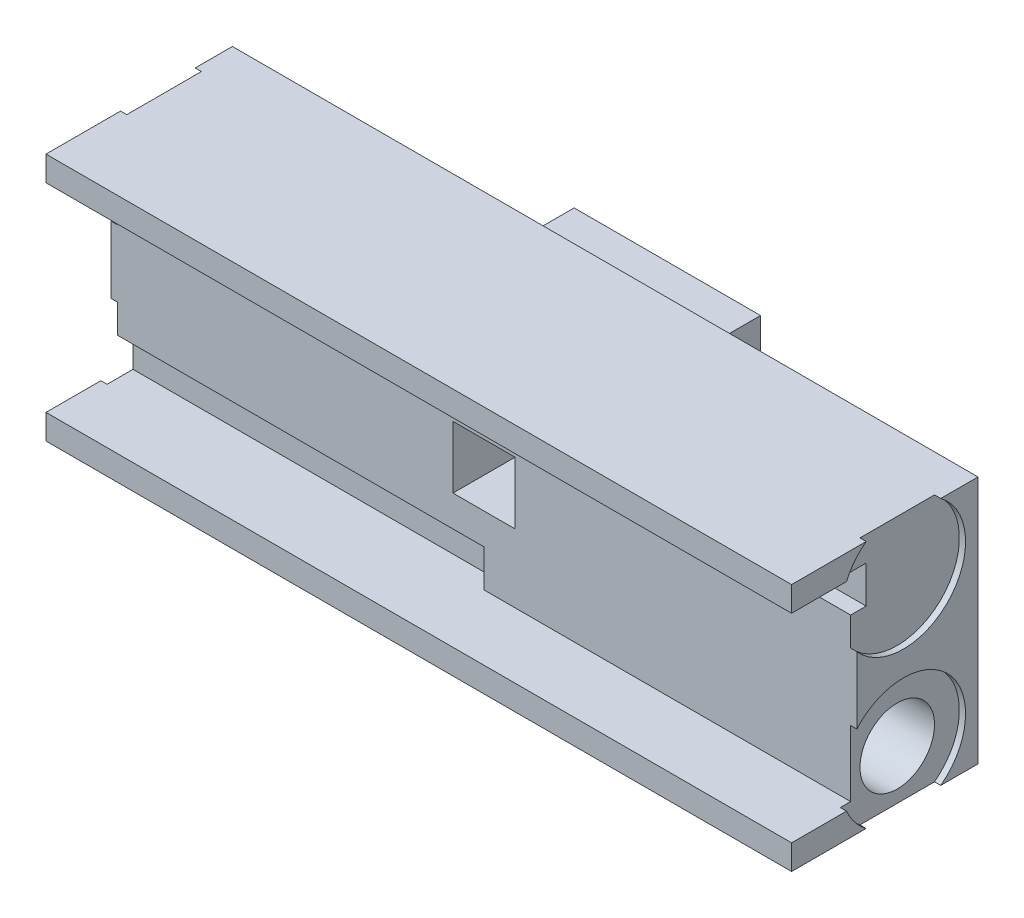
SolidWorks part; units mm, degrees
ref_plane "Front Plane" through (0, 0, 0) normal (0, 0, 1) x (1, 0, 0)
ref_plane "Top Plane" through (0, 0, 0) normal (0, 1, 0) x (1, 0, 0)
ref_plane "Right Plane" through (0, 0, 0) normal (1, 0, 0) x (0, 0, -1)
sketch "Sketch1" plane through (0, 0, 0) normal (0, 0, 1) x (1, 0, 0)
  line L1 (294.0476, 103.9123) -> (414.0476, 103.9123)
  line L2 (294.0476, 103.9123) -> (294.0476, 63.9123)
  line L3 (294.0476, 63.9123) -> (414.0476, 63.9123)
  line L4 (414.0476, 103.9123) -> (414.0476, 63.9123)
  line L5 (294.0476, 103.9123) -> (414.0476, 63.9123) construction
  line L6 (294.0476, 63.9123) -> (414.0476, 103.9123) construction
  point P0 (354.0476, 83.9123)
  dimension "D1" = 120
  dimension "D2" = 40
extrude "Boss-Extrude1" add sketch "Sketch1" along normal blind 30
sketch "Sketch2" plane through (414.0476, 0, 0) normal (1, 0, 0) x (0, 0, -1)
  line L0 (-30, 63.9123) -> (-30, 103.9123) construction
  line L1 (-30, 99.9123) -> (-19.5, 99.9123)
  line L2 (-30, 99.9123) -> (-30, 67.9123)
  line L3 (-30, 67.9123) -> (-19.5, 67.9123)
  line L4 (-19.5, 93.9123) -> (-19.5, 67.9123)
  line L5 (-30, 63.9123) -> (0, 63.9123) construction
  line L6 (-19.5, 99.9123) -> (-17, 99.9123)
  line L8 (-19.5, 93.9123) -> (-17, 93.9123)
  line L9 (-17, 99.9123) -> (-17, 93.9123)
  line L10 (-30, 103.9123) -> (0, 103.9123) construction
  dimension "D1" = 2.5
  dimension "D2" = 6
  dimension "D3" = 2.5
  dimension "D4" = 10.5
  dimension "D5" = 4
  dimension "D6" = 4
extrude "Cut-Extrude1" cut sketch "Sketch2" against normal blind 60
sketch "Sketch5" plane through (294.0476, 0, 0) normal (-1, 0, 0) x (0, 0, 1)
  line L0 (30, 103.9123) -> (30, 63.9123) construction
  line L1 (30, 99.9123) -> (19.5, 99.9123)
  line L2 (30, 99.9123) -> (30, 67.9123)
  line L3 (30, 67.9123) -> (19.5, 67.9123)
  line L4 (19.5, 99.9123) -> (19.5, 73.9123)
  line L5 (30, 63.9123) -> (0, 63.9123) construction
  line L6 (19.5, 67.9123) -> (17, 67.9123)
  line L8 (19.5, 73.9123) -> (17, 73.9123)
  line L9 (17, 67.9123) -> (17, 73.9123)
  line L10 (30, 103.9123) -> (0, 103.9123) construction
  dimension "D1" = 2.5
  dimension "D2" = 6
  dimension "D3" = 4
  dimension "D4" = 10.5
  dimension "D5" = 4
  dimension "D6" = 2.5
extrude "Cut-Extrude2" cut sketch "Sketch5" against normal blind 60
sketch "Sketch6" plane through (0, 0, 0) normal (0, 0, -1) x (-1, 0, 0)
  line L0 (-354.0476, 103.9123) -> (-354.0476, 63.9123) construction
  line L1 (-414.0476, 103.9123) -> (-294.0476, 103.9123) construction
  line L2 (-294.0476, 63.9123) -> (-414.0476, 63.9123) construction
  line L4 (-369.0476, 68.9123) -> (-339.0476, 68.9123)
  line L5 (-369.0476, 68.9123) -> (-369.0476, 98.9123)
  line L6 (-369.0476, 98.9123) -> (-339.0476, 98.9123)
  line L7 (-339.0476, 68.9123) -> (-339.0476, 98.9123)
  line L8 (-369.0476, 68.9123) -> (-339.0476, 98.9123) construction
  line L9 (-369.0476, 98.9123) -> (-339.0476, 68.9123) construction
  point P6 (-354.0476, 83.9123)
  dimension "D1" = 30
  dimension "D2" = 30
extrude "Boss-Extrude2" add sketch "Sketch6" along normal blind 10
sketch "Sketch7" plane through (414.0476, 0, 0) normal (1, 0, 0) x (0, 0, -1)
  line L0 (0, 83.9123) -> (-12, 83.9123) construction
  line L1 (0, 63.9123) -> (0, 103.9123) construction
  line L2 (-12, 83.9123) -> (-12, 95.9123) construction
  line L3 (-12, 95.9123) -> (-12, 70.5258) construction
  circle A0 centre (-12, 95.9123) radius 10
  circle A1 centre (-12, 71.9123) radius 10
  dimension "D1" = 20
  dimension "D2" = 20
  dimension "D4" = 24
  dimension "D3" = 12
  dimension "D5" = 12
extrude "Cut-Extrude3" cut sketch "Sketch7" against normal blind 1
ref_plane "Plane1" through (354.0476, 0, 0) normal (-1, 0, 0) x (0, 0, 1)
mirror "Mirror1" about plane through (354.0476, 0, 0) normal (-1, 0, 0) of "Cut-Extrude3"
sketch "Sketch9" plane through (413.0476, 0, 0) normal (1, 0, 0) x (0, 0, -1)
  line L0 (-12, 81.9123) -> (-12, 63.9123) construction
  line L1 (-18, 63.9123) -> (-6, 63.9123) construction
  line L2 (-2, 71.9123) -> (-19.5, 71.9123) construction
  line L3 (-19.5, 78.5267) -> (-19.5, 67.9123) construction
  arc A0 (-6, 63.9123) -> (-19.5, 78.5267) centre (-12, 71.9123) ccw construction
  arc A1 (-6, 63.9123) -> (-19.5, 78.5267) centre (-12, 71.9123) ccw construction
  circle A3 centre (-12, 71.9123) radius 6
  dimension "D1" = 12
  dimension "D2" = 10
  dimension "D3" = 10
  dimension "D4" = 8
extrude "Cut-Extrude4" cut sketch "Sketch9" against normal blind 35
sketch "Sketch10" plane through (295.0476, 0, 0) normal (-1, 0, 0) x (0, 0, 1)
  line L0 (18, 103.9123) -> (6, 103.9123) construction
  circle A0 centre (12, 95.9123) radius 6
  arc A1 (6, 103.9123) -> (19.5, 89.2979) centre (12, 95.9123) ccw construction
  dimension "D1" = 12
  dimension "D3" = 0
  dimension "D2" = 8
extrude "Cut-Extrude5" cut sketch "Sketch10" against normal blind 35
sketch "Sketch11" plane through (0, 0, 19.5) normal (0, 0, 1) x (1, 0, 0)
  line L0 (354.0476, 93.9123) -> (354.0476, 73.9123) construction
  line L1 (349.0476, 88.9123) -> (359.0476, 88.9123)
  line L2 (349.0476, 88.9123) -> (349.0476, 78.9123)
  line L3 (349.0476, 78.9123) -> (359.0476, 78.9123)
  line L4 (359.0476, 88.9123) -> (359.0476, 78.9123)
  line L5 (349.0476, 88.9123) -> (359.0476, 78.9123) construction
  line L6 (349.0476, 78.9123) -> (359.0476, 88.9123) construction
  line L7 (354.0476, 83.9123) -> (374.0476, 83.9123) construction
  dimension "D1" = 20
  dimension "D2" = 10
  dimension "D3" = 10
  dimension "D5" = 5
  dimension "D6" = 5
  dimension "D7" = 10
  dimension "D8" = 10
extrude "Cut-Extrude6" cut sketch "Sketch11" against normal blind 10
